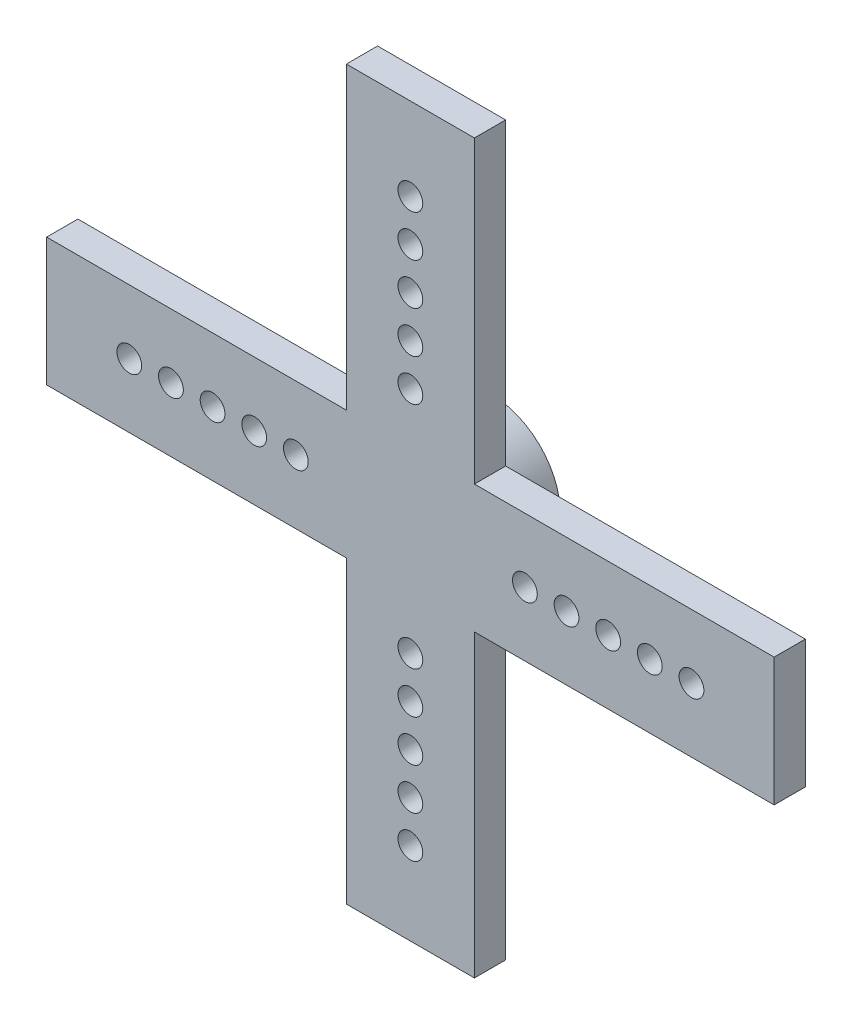
SolidWorks part; units mm, degrees
ref_plane "Front Plane" through (0, 0, 0) normal (0, 0, 1) x (1, 0, 0)
ref_plane "Top Plane" through (0, 0, 0) normal (0, 1, 0) x (1, 0, 0)
ref_plane "Right Plane" through (0, 0, 0) normal (1, 0, 0) x (0, 0, -1)
sketch "Sketch1" plane through (0, 0, 0) normal (0, 0, 1) x (1, 0, 0)
  line L1 (-22.1869, -22.1869) -> (22.1869, -22.1869)
  line L2 (-22.1869, -22.1869) -> (-22.1869, 22.1869)
  line L3 (-22.1869, 22.1869) -> (22.1869, 22.1869)
  line L4 (22.1869, -22.1869) -> (22.1869, 22.1869)
  line L5 (-22.1869, -22.1869) -> (22.1869, 22.1869) construction
  line L6 (-22.1869, 22.1869) -> (22.1869, -22.1869) construction
  point P0 (0, 0)
extrude "Extrude1" add sketch "Sketch1" along normal blind 1.905
sketch "Sketch2" plane through (0, 0, 0) normal (0, 0, -1) x (-1, 0, 0)
  circle A0 centre (0, 0) radius 4.2291
  circle A1 centre (0, 0) radius 2.9718
extrude "Extrude2" add sketch "Sketch2" along normal blind 3.0226
sketch "Sketch3" plane through (0, 0, 1.905) normal (0, 0, 1) x (1, 0, 0)
  line L0 (0, 0) -> (6.985, 0) construction
  line L1 (0, 0) -> (0, 22.1869) construction
  line L2 (22.1869, 22.1869) -> (-22.1869, 22.1869) construction
hole_wizard "#53 (0.0595) Diameter Hole1" positions "3DSketch1" profile "Sketch4" hole size "#53" standard "Ansi Inch"
sketch3d "3DSketch1"
  point P0 (6.985, 0, 1.905)
sketch "Sketch4" plane through (6.985, 0, 1.905) normal (1, 0, 0) x (0, -1, 0)
  line L0 (0, 0) -> (0, 5.534)
  line L1 (0, 5.534) -> (0.7556, 5.08)
  line L2 (0.7556, 5.08) -> (0.7556, 0)
  line L5 (0.7556, 0) -> (0, 0)
  line L10 (0, 5.534) -> (-0.7557, 5.08) construction
  line L11 (0, -6.35) -> (0, 107.95) construction
  dimension "Hole Dia." = 1.5113
  dimension "Hole Depth" = 5.08
  dimension "Drill Angle" = 118
pattern_linear "LPattern2" count 5 spacing 2.54 along (1, 0, 0) of "#53 (0.0595) Diameter Hole1"
pattern_circular "CirPattern2" count 4 over 360 about axis through (0, 0, 0) along (0, 0, 1) of "LPattern2", "#53 (0.0595) Diameter Hole1"
sketch "Sketch6" plane through (0, 0, 1.905) normal (0, 0, 1) x (1, 0, 0)
  line L0 (0, 0) -> (-3.9044, 3.9044) construction
  line L2 (-3.9044, 3.9044) -> (-22.1869, 3.9044)
  line L3 (-3.9044, 3.9044) -> (-3.9044, 22.1869)
  line L4 (-3.9044, 22.1869) -> (-22.1869, 22.1869)
  line L5 (-22.1869, 3.9044) -> (-22.1869, 22.1869)
extrude "Extrude3" cut sketch "Sketch6" against normal through all
pattern_circular "CirPattern3" count 4 over 360 about axis through (0, 0, 0) along (0, 0, 1) of "Extrude3"
